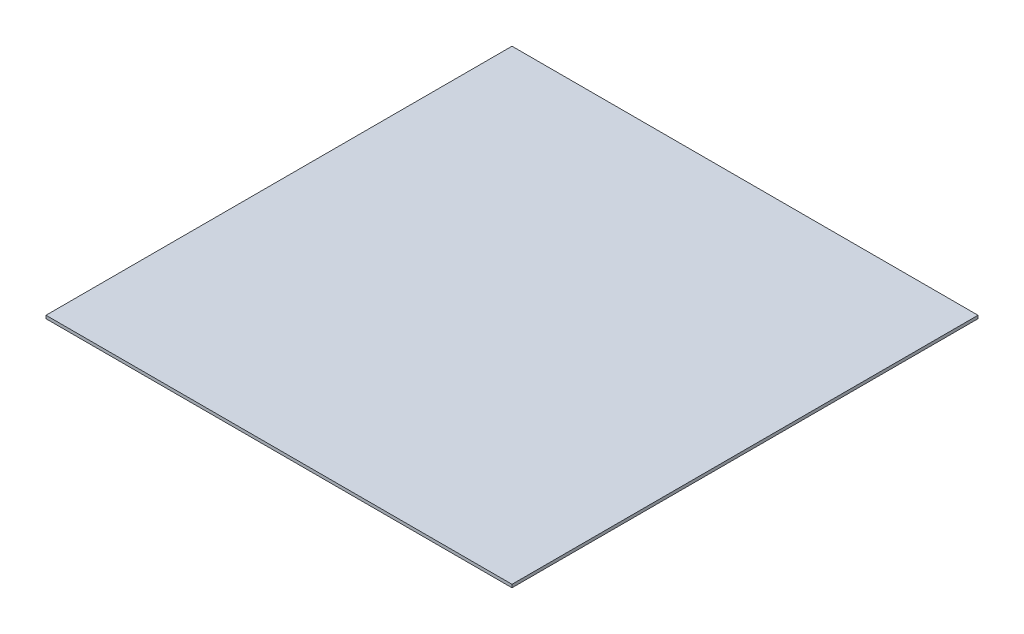
SolidWorks part; units mm, degrees
ref_plane "Front Plane" through (0, 0, 0) normal (0, 0, 1) x (1, 0, 0)
ref_plane "Top Plane" through (0, 0, 0) normal (0, 1, 0) x (1, 0, 0)
ref_plane "Right Plane" through (0, 0, 0) normal (1, 0, 0) x (0, 0, -1)
sketch "Sketch1" plane through (0, 0, 0) normal (0, 1, 0) x (1, 0, 0)
  line L1 (-152.4, 152.4) -> (152.4, 152.4)
  line L2 (-152.4, 152.4) -> (-152.4, -152.4)
  line L3 (-152.4, -152.4) -> (152.4, -152.4)
  line L4 (152.4, 152.4) -> (152.4, -152.4)
  point P4 (0, 152.4)
  point P6 (-152.4, 0)
  dimension "D1" = 304.8
  dimension "D2" = 304.8
extrude "Boss-Extrude1" add sketch "Sketch1" along normal blind 2
